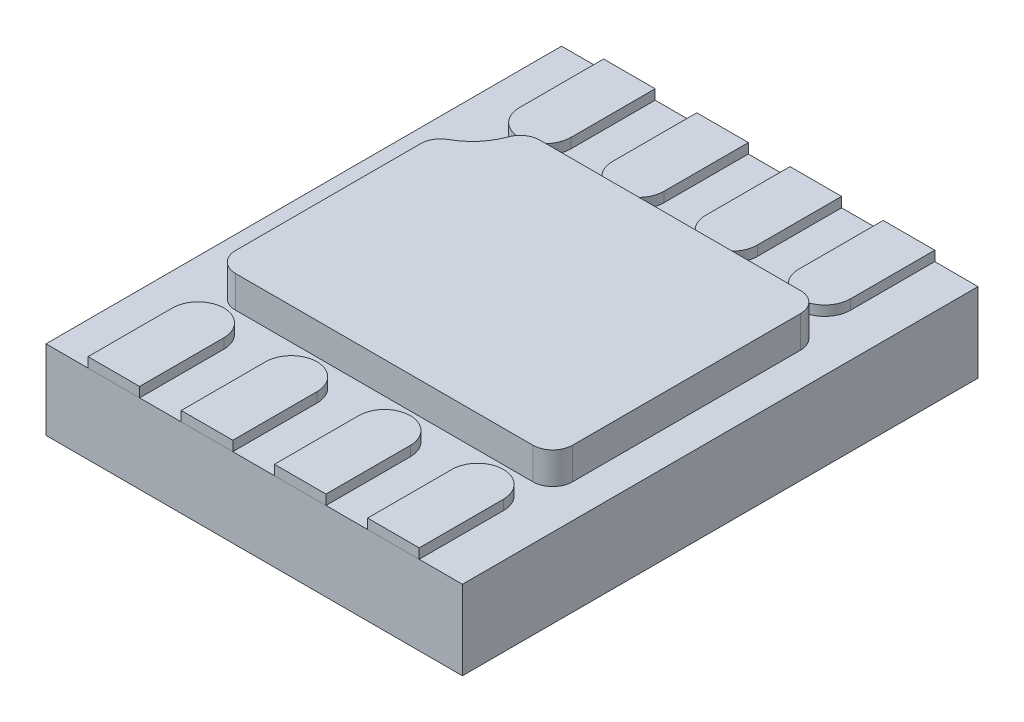
SolidWorks part; units mm, degrees
ref_plane "Front Plane" through (0, 0, 0) normal (0, 0, 1) x (1, 0, 0)
ref_plane "Top Plane" through (0, 0, 0) normal (0, 1, 0) x (1, 0, 0)
ref_plane "Right Plane" through (0, 0, 0) normal (1, 0, 0) x (0, 0, -1)
sketch "Sketch1" plane through (0, 0, 0) normal (0, 1, 0) x (1, 0, 0)
  line L1 (-1.05, -1.3) -> (1.05, -1.3)
  line L2 (-1.05, -1.3) -> (-1.05, 1.3)
  line L3 (-1.05, 1.3) -> (1.05, 1.3)
  line L4 (1.05, -1.3) -> (1.05, 1.3)
  line L5 (-1.05, -1.3) -> (1.05, 1.3) construction
  line L6 (-1.05, 1.3) -> (1.05, -1.3) construction
  point P0 (0, 0)
  dimension "D1" = 2.1
  dimension "D2" = 2.6
extrude "Boss-Extrude1" add sketch "Sketch1" along normal blind 0.4
sketch "Sketch2" plane through (0, 0.4, 0) normal (0, 1, 0) x (1, 0, 0)
  line L0 (-0.8196, 0.3594) -> (-0.8196, -0.575)
  line L1 (-0.7196, -0.675) -> (0.7804, -0.675)
  line L2 (0.8804, -0.575) -> (0.8804, 0.575)
  line L3 (0.7804, 0.675) -> (-0.5344, 0.675)
  line L5 (1.05, 1.3) -> (-1.05, 1.3) construction
  arc A0 (-0.7674, 0.4473) -> (-0.6284, 0.609) centre (-0.9106, 0.7109) ccw
  arc A1 (-0.7674, 0.4473) -> (-0.8196, 0.3594) centre (-0.7196, 0.3594) ccw
  arc A2 (-0.8196, -0.575) -> (-0.7196, -0.675) centre (-0.7196, -0.575) ccw
  arc A3 (0.7804, -0.675) -> (0.8804, -0.575) centre (0.7804, -0.575) ccw
  arc A4 (0.8804, 0.575) -> (0.7804, 0.675) centre (0.7804, 0.575) ccw
  arc A5 (-0.5344, 0.675) -> (-0.6284, 0.609) centre (-0.5344, 0.575) ccw
  point P6 (0, 0)
  point P7 (0, 0)
  point P10 (-0.8196, 0.425)
  point P13 (-0.8196, -0.675)
  point P16 (0.8804, -0.675)
  point P19 (0.8804, 0.675)
  dimension "D4" = 0.3
  dimension "D5" = 0.1
  dimension "D1" = 1.7
  dimension "D2" = 1.35
  dimension "D3" = 1.1
  dimension "D6" = 0.625
extrude "Boss-Extrude2" add sketch "Sketch2" along normal blind 0.16
sketch "Sketch3" plane through (0, 0.4, 0) normal (0, 1, 0) x (1, 0, 0)
  line L0 (-1.05, -1.3) -> (1.05, -1.3) construction
  line L1 (-0.838, -1.3) -> (-0.578, -1.3)
  line L2 (-0.838, -1.3) -> (-0.838, -0.875)
  line L3 (-0.838, -0.875) -> (-0.578, -0.875)
  line L4 (-0.578, -1.3) -> (-0.578, -0.875)
  line L5 (-0.368, -1.3) -> (-0.368, -0.875)
  line L6 (-0.7196, -0.675) -> (0.7804, -0.675) construction
  line L19 (-1.05, 1.3) -> (-1.05, -1.3) construction
  line L20 (-0.368, -1.3) -> (-0.108, -1.3)
  line L21 (-0.108, -1.3) -> (-0.108, -0.875)
  line L22 (-0.368, -0.875) -> (-0.108, -0.875)
  line L23 (0.102, -1.3) -> (0.102, -0.875)
  line L24 (0.102, -1.3) -> (0.362, -1.3)
  line L25 (0.362, -1.3) -> (0.362, -0.875)
  line L26 (0.102, -0.875) -> (0.362, -0.875)
  line L27 (0.572, -1.3) -> (0.572, -0.875)
  line L28 (0.572, -1.3) -> (0.832, -1.3)
  line L29 (0.832, -1.3) -> (0.832, -0.875)
  line L30 (0.572, -0.875) -> (0.832, -0.875)
  circle A0 centre (-0.708, -0.875) radius 0.13
  circle A4 centre (-0.238, -0.875) radius 0.13
  circle A5 centre (0.232, -0.875) radius 0.13
  circle A6 centre (0.702, -0.875) radius 0.13
  line M24 (-1.05, -1.3) -> (1.05, -1.3)
  dimension "D3" = 4
  dimension "D1" = 0.2
  dimension "D2" = 0.26
  dimension "D4" = 0.212
ref_plane "Plane1" through (0, 0, 0) normal (0, 0, -1) x (-1, 0, 0)
extrude "Boss-Extrude3" add sketch "Sketch3" along normal blind 0.05 separate body contours A4 L5 L21 M24 | L22 A4 | L22 A4 | L3 A0 | L3 A0 | A0 L2 L4 M24 | A5 L23 L25 M24 | L26 A5 | L26 A5 | A6 L27 L29 M24 | L30 A6 | L30 A6
mirror "Mirror1" about plane through (0, 0, 0) normal (0, 0, -1) of "Boss-Extrude3"
